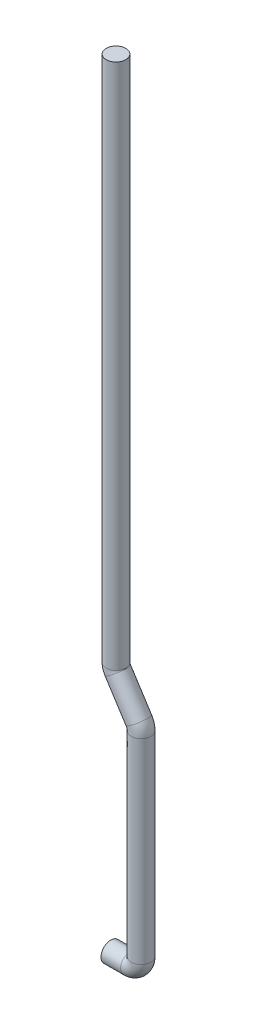
SolidWorks part; units mm, degrees
material "Copper"
ref_plane "Front Plane" through (0, 0, 0) normal (0, 0, 1) x (1, 0, 0)
ref_plane "Top Plane" through (0, 0, 0) normal (0, 1, 0) x (1, 0, 0)
ref_plane "Right Plane" through (0, 0, 0) normal (1, 0, 0) x (0, 0, -1)
sketch "Sketch3" plane through (0, 0, 0) normal (0, 0, 1) x (1, 0, 0)
  line L0 (0, 0) -> (8, 0)
  line L1 (12.3505, 4.3505) -> (12.3505, 84.0315)
  line L2 (11.3884, 87.3076) -> (2.8031, 100.6628)
  line L8 (2.1121, 317.7217) -> (2.1121, 103.0154)
  arc A1 (8, 0) -> (12.3505, 4.3505) centre (8, 4.3505) ccw
  arc A3 (12.3505, 84.0315) -> (11.3884, 87.3076) centre (6.2921, 84.0315) ccw
  arc A4 (2.8031, 100.6628) -> (2.1121, 103.0154) centre (6.4627, 103.0154) cw
  point P6 (1.5705, 341.9264)
  point P7 (2.1121, 317.7217)
  point P15 (2, 8)
  point P18 (12.3505, 0)
  point P21 (2, 85.8109)
  point P24 (12.3505, 85.8109)
  dimension "D1" = 4.3505
  dimension "D2" = 8
sketch "Sketch17" plane through (0, 0, 0) normal (1, 0, 0) x (0, 0, -1)
  circle A0 centre (0, 0) radius 4
sweep "Sweep22" add profiles "Sketch17" path "Sketch3"
